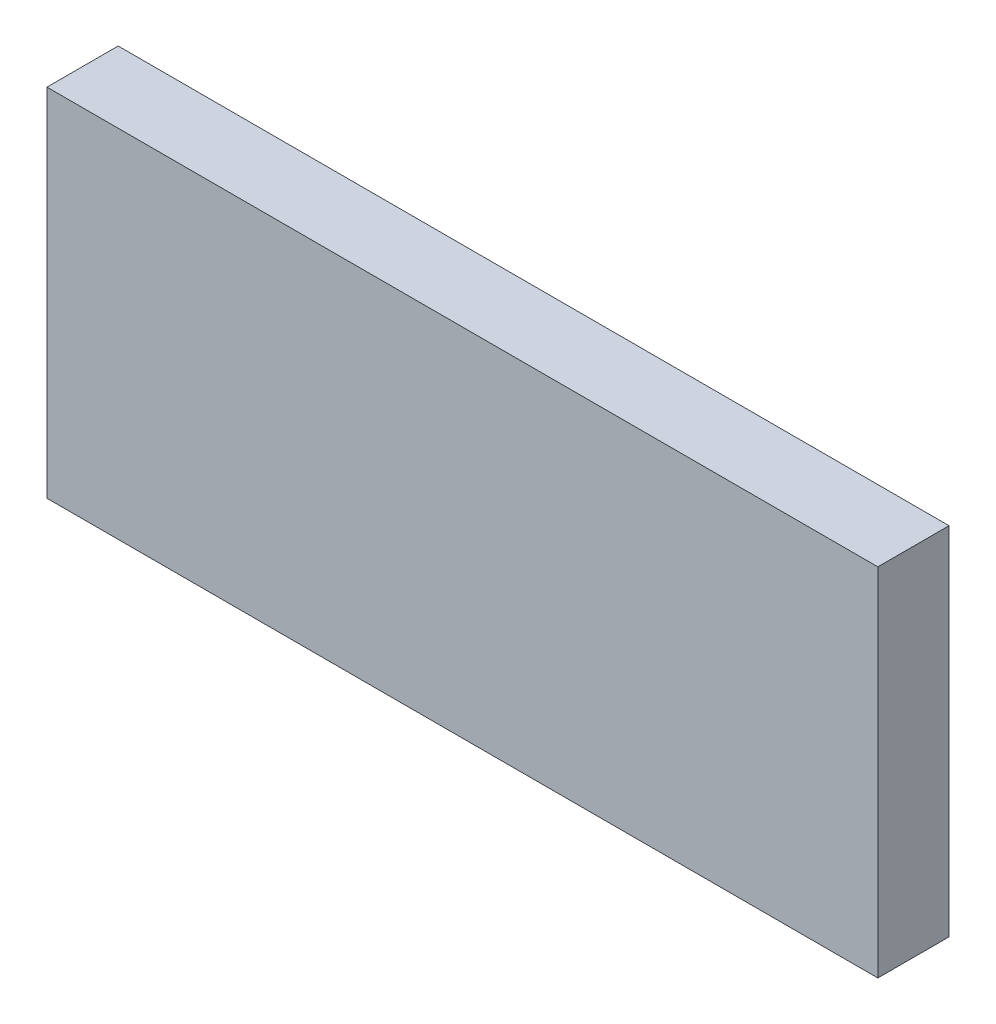
SolidWorks part; units mm, degrees
ref_plane "Alzado" through (0, 0, 0) normal (0, 0, 1) x (1, 0, 0)
ref_plane "Planta" through (0, 0, 0) normal (0, 1, 0) x (1, 0, 0)
ref_plane "Vista lateral" through (0, 0, 0) normal (1, 0, 0) x (0, 0, -1)
sketch "Croquis1" plane through (0, 0, 0) normal (0, 0, 1) x (1, 0, 0)
  line L1 (-17.5, -7.5) -> (17.5, -7.5)
  line L2 (-17.5, -7.5) -> (-17.5, 7.5)
  line L3 (-17.5, 7.5) -> (17.5, 7.5)
  line L4 (17.5, -7.5) -> (17.5, 7.5)
  line L5 (-17.5, -7.5) -> (17.5, 7.5) construction
  line L6 (-17.5, 7.5) -> (17.5, -7.5) construction
  point P0 (0, 0)
  dimension "D1" = 35
  dimension "D2" = 15
extrude "Saliente-Extruir1" add sketch "Croquis1" along normal blind 3
